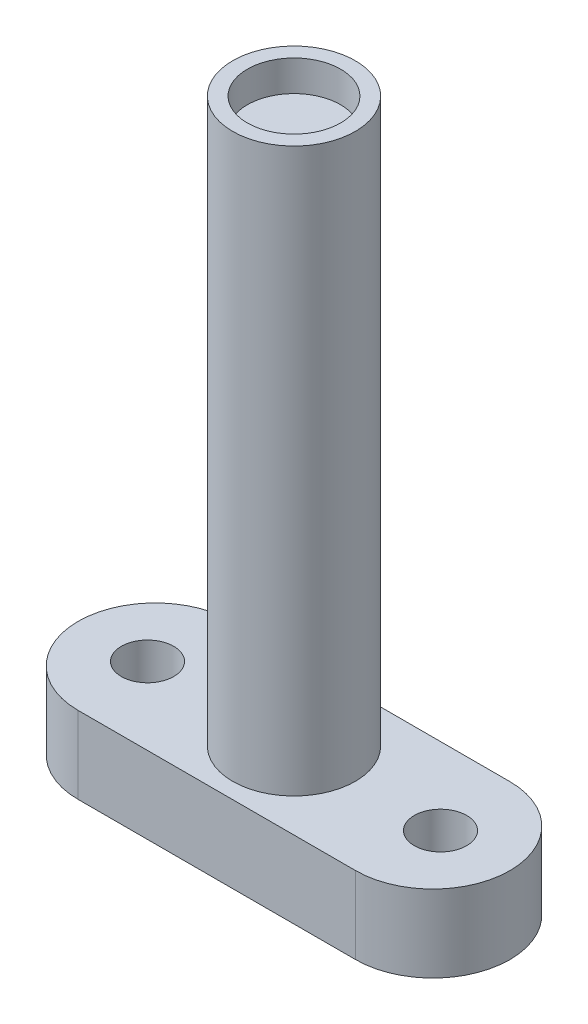
SolidWorks part; units mm, degrees
ref_plane "Front Plane" through (0, 0, 0) normal (0, 0, 1) x (1, 0, 0)
ref_plane "Top Plane" through (0, 0, 0) normal (0, 1, 0) x (1, 0, 0)
ref_plane "Right Plane" through (0, 0, 0) normal (1, 0, 0) x (0, 0, -1)
sketch "Sketch1" plane through (0, 0, 0) normal (0, 1, 0) x (1, 0, 0)
  line L0 (-9, 0) -> (9, 0) construction
  line L1 (-9, 5) -> (9, 5)
  line L2 (-9, -5) -> (9, -5)
  arc A0 (-9, 5) -> (-9, -5) centre (-9, 0) ccw
  arc A1 (9, -5) -> (9, 5) centre (9, 0) ccw
  point P3 (0, 0)
  dimension "D2" = 5
  dimension "D1" = 18
extrude "Boss-Extrude1" add sketch "Sketch1" along normal blind 5
hole_wizard "M3 Clearance Hole1" positions "Sketch2" profile "Sketch3" hole size "M3" standard "ANSI Metric"
sketch "Sketch2" plane through (0, 5, 0) normal (0, 1, 0) x (1, 0, 0)
  line L0 (-9.5, 0) -> (9.5, 0) construction
  point P0 (-9.5, 0)
  point P2 (9.5, 0)
  point P9 (0, 0)
  dimension "D1" = 19
sketch "Sketch3" plane through (-9.5, 5, 0) normal (1, 0, 0) x (0, 0, 1)
  line L0 (0, 0) -> (0, 6.0215)
  line L1 (0, 6.0215) -> (1.7, 5)
  line L2 (1.7, 5) -> (1.7, 0)
  line L5 (1.7, 0) -> (0, 0)
  line L10 (0, 6.0215) -> (-1.7, 5) construction
  line L11 (0, -6.35) -> (0, 107.95) construction
  dimension "Hole Dia." = 3.4
  dimension "Hole Depth" = 5
  dimension "Drill Angle" = 118
sketch "Sketch4" plane through (0, 5, 0) normal (0, 1, 0) x (1, 0, 0)
  circle A0 centre (0, 0) radius 3.975
  dimension "D1" = 7.95
extrude "Boss-Extrude2" add sketch "Sketch4" along normal blind 36.5
sketch "Sketch5" plane through (0, 41.5, 0) normal (0, 1, 0) x (1, 0, 0)
  circle A0 centre (0, 0) radius 3.025
  dimension "D1" = 6.05
extrude "Cut-Extrude1" cut sketch "Sketch5" against normal blind 2
